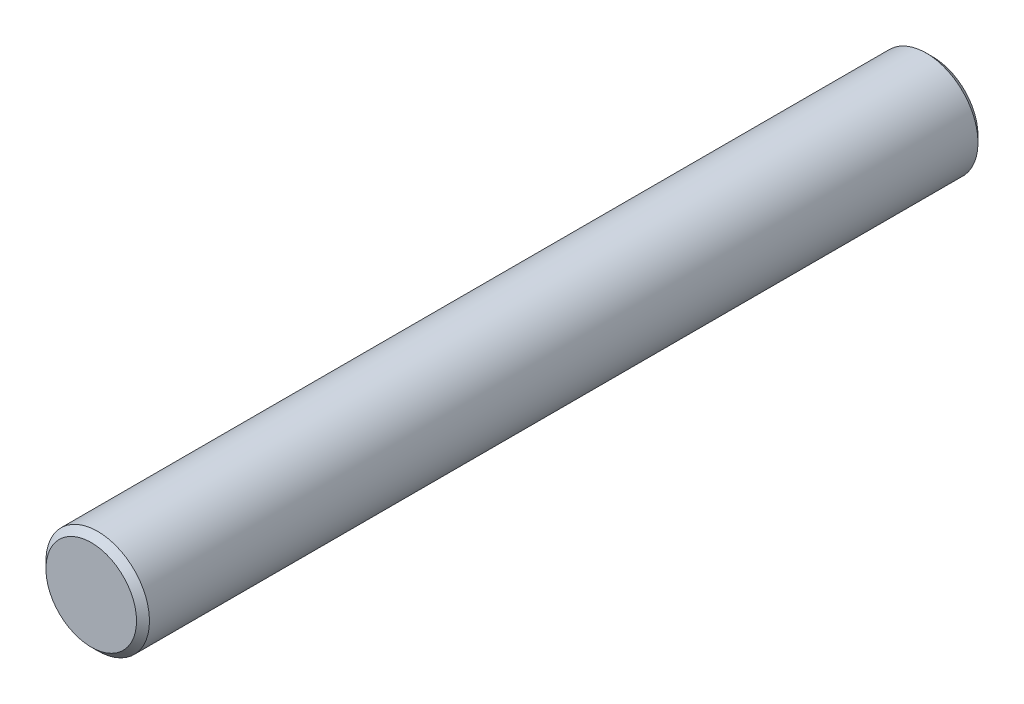
SolidWorks part; units mm, degrees
ref_plane "Plan de face" through (0, 0, 0) normal (0, 0, 1) x (1, 0, 0)
ref_plane "Plan de dessus" through (0, 0, 0) normal (0, 1, 0) x (1, 0, 0)
ref_plane "Plan de droite" through (0, 0, 0) normal (1, 0, 0) x (0, 0, -1)
sketch "Esquisse1" plane through (0, 0, 0) normal (0, 0, 1) x (1, 0, 0)
  circle A0 centre (0, 0) radius 4
  dimension "D1" = 8
extrude "Boss.-Extru.1" add sketch "Esquisse1" along normal blind 65
chamfer "Chanfrein1" distance 0.5 angle 45 2 edges at (4, 0, 65) (4, 0, 0)
